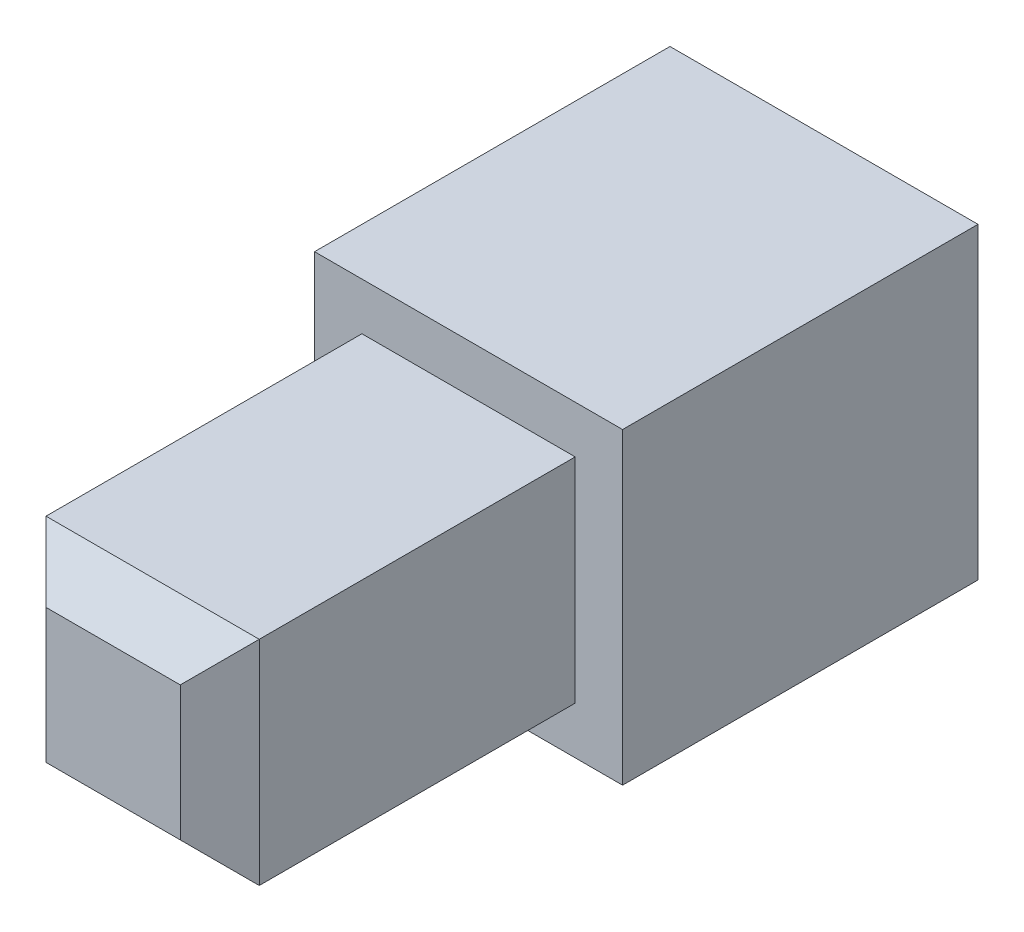
SolidWorks part; units mm, degrees
ref_plane "Front Plane" through (0, 0, 0) normal (0, 0, 1) x (1, 0, 0)
ref_plane "Top Plane" through (0, 0, 0) normal (0, 1, 0) x (1, 0, 0)
ref_plane "Right Plane" through (0, 0, 0) normal (1, 0, 0) x (0, 0, -1)
sketch "Sketch2" plane through (0, 0, 100.3354) normal (0, 0, 1) x (1, 0, 0)
  line L0 (-15.0508, 92.6158) -> (-15.0508, 87.4158) construction
  line L1 (-16.0508, 93.9158) -> (-8.2508, 93.9158)
  line L2 (-16.0508, 93.9158) -> (-16.0508, 86.1158)
  line L3 (-16.0508, 86.1158) -> (-8.2508, 86.1158)
  line L4 (-8.2508, 93.9158) -> (-8.2508, 86.1158)
  line L5 (-9.5508, 92.9158) -> (-14.7508, 92.9158) construction
  line L6 (-9.2508, 87.4158) -> (-9.2508, 92.6158) construction
  line L7 (-14.7508, 87.1158) -> (-9.5508, 87.1158) construction
  dimension "D1" = 1
  dimension "D2" = 1
  dimension "D3" = 1
  dimension "D4" = 1
extrude "Boss-Extrude1" add sketch "Sketch2" along normal blind 5
sketch "Sketch3" plane through (0, 0, 100.3354) normal (0, 0, -1) x (-1, 0, 0)
  line L0 (16.0508, 93.9158) -> (16.0508, 86.1158) construction
  line L1 (16.0508, 86.1158) -> (8.2508, 86.1158) construction
  line L2 (8.2508, 86.1158) -> (8.2508, 93.9158) construction
  line L3 (8.2508, 93.9158) -> (16.0508, 93.9158) construction
  line L4 (16.0508, 93.9158) -> (16.0508, 86.1158)
  line L5 (16.0508, 86.1158) -> (8.2508, 86.1158)
  line L6 (8.2508, 86.1158) -> (8.2508, 93.9158)
  line L7 (8.2508, 93.9158) -> (16.0508, 93.9158)
  line L8 (9.0508, 93.1158) -> (15.2508, 93.1158)
  line L9 (15.2508, 93.1158) -> (15.2508, 86.9158)
  line L10 (15.2508, 86.9158) -> (9.0508, 86.9158)
  line L11 (9.0508, 86.9158) -> (9.0508, 93.1158)
  dimension "D1" = 0.8
extrude "Boss-Extrude2" add sketch "Sketch3" along normal blind 4
sketch "Sketch4" plane through (0, 0, 105.3354) normal (0, 0, 1) x (1, 0, 0)
  line L0 (-9.1508, 93.0158) -> (-15.1508, 93.0158) construction
  line L1 (-14.8508, 92.7158) -> (-9.4508, 92.7158)
  line L2 (-14.8508, 92.7158) -> (-14.8508, 87.3158)
  line L3 (-14.8508, 87.3158) -> (-9.4508, 87.3158)
  line L4 (-9.4508, 92.7158) -> (-9.4508, 87.3158)
  line L5 (-15.1508, 93.0158) -> (-15.1508, 87.0158) construction
  line L6 (-15.1508, 87.0158) -> (-9.1508, 87.0158) construction
  line L7 (-9.1508, 87.0158) -> (-9.1508, 93.0158) construction
  dimension "D1" = 0.3
  dimension "D2" = 0.3
  dimension "D3" = 0.3
  dimension "D4" = 0.3
extrude "Boss-Extrude3" add sketch "Sketch4" along normal blind 9
chamfer "Chamfer1" distance 1 angle 45 4 edges at (-12.1508, 92.7158, 114.3354) (-9.4508, 90.0158, 114.3354) (-12.1508, 87.3158, 114.3354) (-14.8508, 90.0158, 114.3354)
